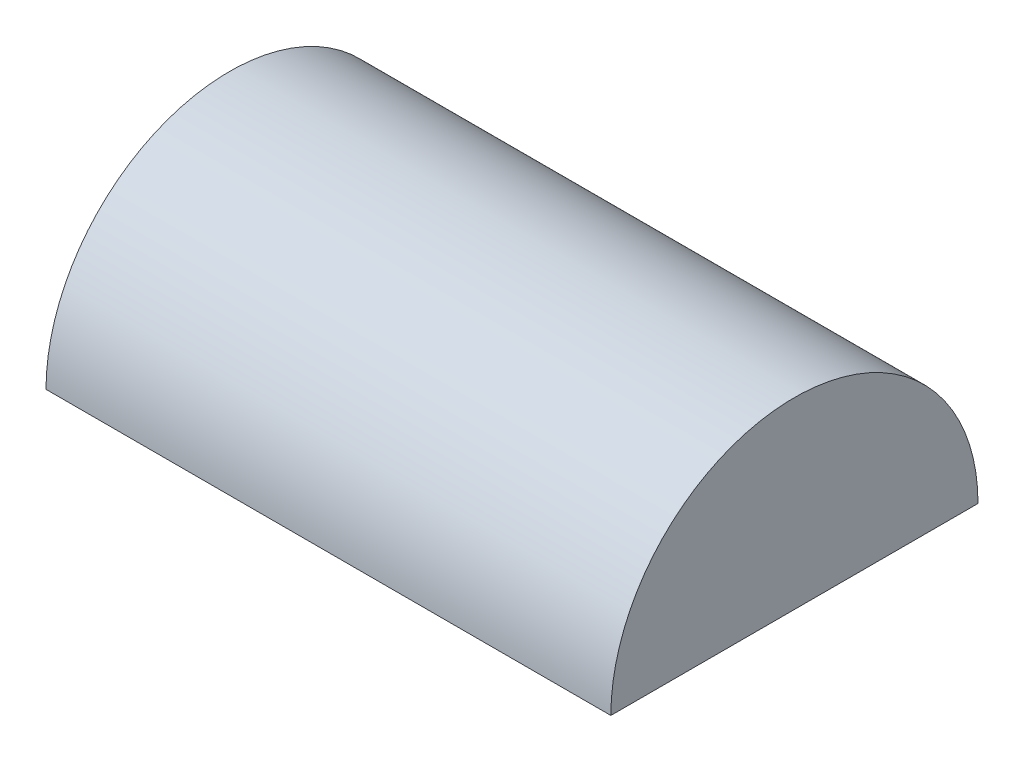
SolidWorks part; units mm, degrees
ref_plane "Front Plane" through (0, 0, 0) normal (0, 0, 1) x (1, 0, 0)
ref_plane "Top Plane" through (0, 0, 0) normal (0, 1, 0) x (1, 0, 0)
ref_plane "Right Plane" through (0, 0, 0) normal (1, 0, 0) x (0, 0, -1)
sketch "Sketch1" plane through (0, 0, 0) normal (1, 0, 0) x (0, 0, -1)
  circle A0 centre (0, 0) radius 19.5
  dimension "D1" = 39
extrude "Boss-Extrude1" add sketch "Sketch1" along normal blind 60
sketch "Sketch2" plane through (0, 0, 0) normal (1, 0, 0) x (0, 0, -1)
  line L0 (23.5745, 0) -> (-23.5745, 0) construction
  line L1 (-21.3977, 0) -> (21.4652, 0)
  line L2 (-21.3977, 0) -> (-21.3977, -22.9164)
  line L3 (-21.3977, -22.9164) -> (21.4652, -22.9164)
  line L4 (21.4652, 0) -> (21.4652, -22.9164)
extrude "Cut-Extrude2" cut sketch "Sketch2" along normal blind 101
